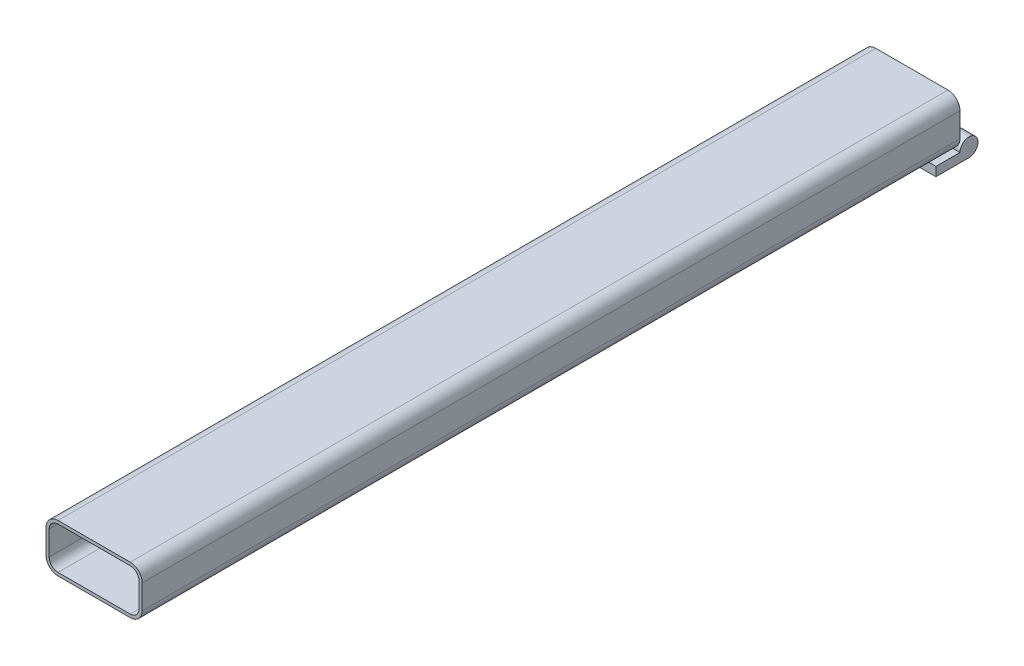
SolidWorks part; units mm, degrees
ref_plane "Front Plane" through (0, 0, 0) normal (0, 0, 1) x (1, 0, 0)
ref_plane "Top Plane" through (0, 0, 0) normal (0, 1, 0) x (1, 0, 0)
ref_plane "Right Plane" through (0, 0, 0) normal (1, 0, 0) x (0, 0, -1)
sketch "Sketch1" plane through (0, 0, 0) normal (0, 0, 1) x (1, 0, 0)
  line L0 (-19.05, 11.049) -> (19.05, 11.049)
  line L1 (-19.05, -12.7) -> (19.05, -12.7)
  line L2 (-25.4, -6.35) -> (-25.4, 6.35)
  line L3 (-19.05, 12.7) -> (19.05, 12.7)
  line L4 (25.4, -6.35) -> (25.4, 6.35)
  line L5 (-25.4, -12.7) -> (25.4, 12.7) construction
  line L6 (-25.4, 12.7) -> (25.4, -12.7) construction
  line L7 (23.749, -6.35) -> (23.749, 6.35)
  line L8 (-19.05, -11.049) -> (19.05, -11.049)
  line L9 (-23.749, -6.35) -> (-23.749, 6.35)
  arc A0 (-19.05, -12.7) -> (-25.4, -6.35) centre (-19.05, -6.35) cw
  arc A1 (19.05, -12.7) -> (25.4, -6.35) centre (19.05, -6.35) ccw
  arc A2 (19.05, 12.7) -> (25.4, 6.35) centre (19.05, 6.35) cw
  arc A3 (-25.4, 6.35) -> (-19.05, 12.7) centre (-19.05, 6.35) cw
  arc A4 (-23.749, 6.35) -> (-19.05, 11.049) centre (-19.05, 6.35) cw
  arc A5 (19.05, 11.049) -> (23.749, 6.35) centre (19.05, 6.35) cw
  arc A6 (19.05, -11.049) -> (23.749, -6.35) centre (19.05, -6.35) ccw
  arc A7 (-19.05, -11.049) -> (-23.749, -6.35) centre (-19.05, -6.35) cw
  point P0 (0, 0)
  dimension "D3" = 6.35
  dimension "D1" = 50.8
  dimension "D2" = 25.4
  dimension "D4" = 1.651
extrude "Boss-Extrude1" add sketch "Sketch1" along normal mid plane 431.8
sketch "Sketch2" plane through (25.4, 0, 0) normal (1, 0, 0) x (0, 0, -1)
  line L0 (203.2, -12.7) -> (203.2, -17.4625)
  line L1 (-215.9, -12.7) -> (215.9, -12.7) construction
  line L2 (203.2, -17.4625) -> (220.6625, -17.4625)
  line L3 (215.9, -12.7) -> (215.9, -6.35) construction
  line L4 (215.9, -6.35) -> (215.9, 6.35) construction
  line L5 (215.9, -12.7) -> (203.2, -12.7)
  arc A0 (220.6625, -17.4625) -> (215.9, -12.7) centre (220.6625, -12.7) ccw
  dimension "D1" = 4.7625
  dimension "D2" = 4.7625
  dimension "D3" = 12.7
extrude "Boss-Extrude2" add sketch "Sketch2" against normal through all
sketch "Sketch4" plane through (0, -17.4625, 0) normal (0, -1, 0) x (1, 0, 0)
  line L0 (-9.525, -225.425) -> (-9.525, -215.9)
  line L1 (-25.4, -225.425) -> (25.4, -225.425) construction
  line L2 (-9.525, -215.9) -> (9.525, -215.9)
  line L3 (9.525, -215.9) -> (9.525, -225.425)
  line L4 (-25.4, -225.425) -> (25.4, -225.425) construction
  line L5 (9.525, -225.425) -> (-9.525, -225.425)
  line L6 (0, -215.9) -> (0, -225.425) construction
  line L7 (25.4, -203.2) -> (25.4, -220.6625) construction
  line L8 (-25.4, -203.2) -> (-25.4, -220.6625) construction
  dimension "D1" = 19.05
  dimension "D2" = 9.525
extrude "Cut-Extrude1" cut sketch "Sketch4" against normal through all
sketch "Sketch3" plane through (0, 0, 0) normal (1, 0, 0) x (0, 0, -1)
  circle A0 centre (220.6625, -12.7) radius 3.175
  dimension "D1" = 6.35
extrude "Boss-Extrude3" add sketch "Sketch3" along normal mid plane 38.1
